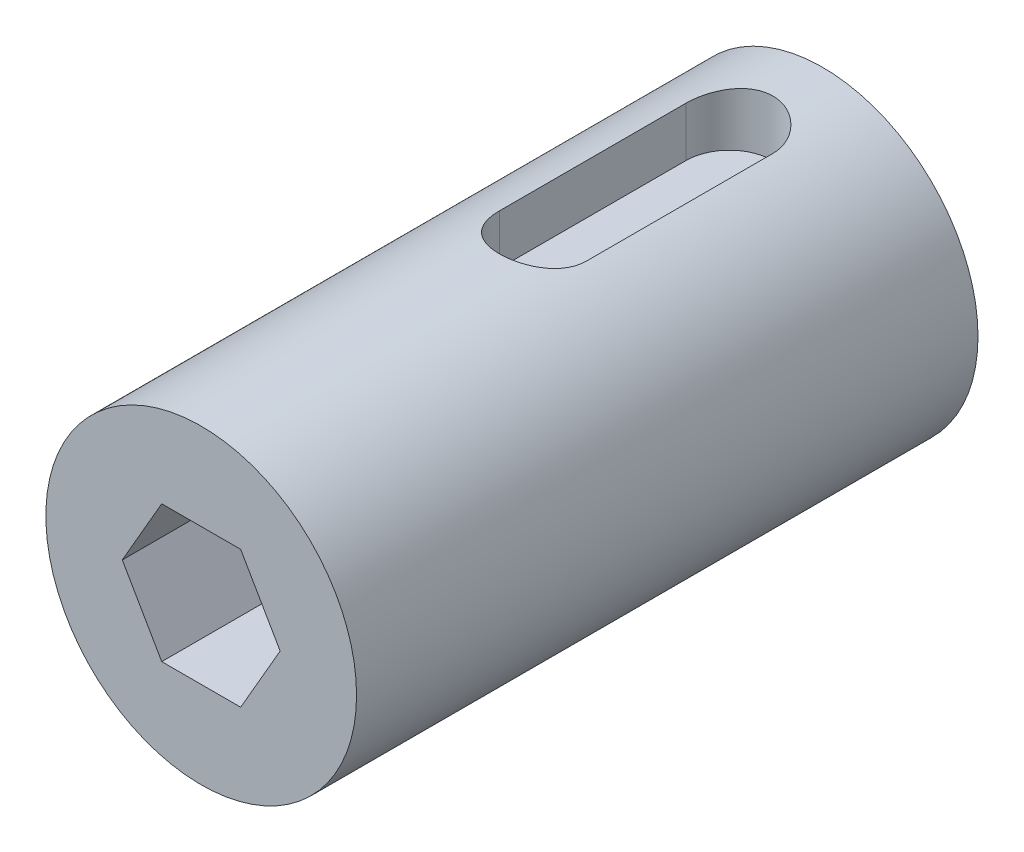
SolidWorks part; units mm, degrees
ref_plane "Piano frontale" through (0, 0, 0) normal (0, 0, 1) x (1, 0, 0)
ref_plane "Piano superiore" through (0, 0, 0) normal (0, 1, 0) x (1, 0, 0)
ref_plane "Piano destro" through (0, 0, 0) normal (1, 0, 0) x (0, 0, -1)
sketch "Schizzo1" plane through (0, 0, 0) normal (0, 0, 1) x (1, 0, 0)
  circle A0 centre (0, 0) radius 12.5
  dimension "D1" = 25
extrude "Estrusione-Estrusione1" add sketch "Schizzo1" along normal blind 50
sketch "Schizzo2" plane through (0, 0, 50) normal (0, 0, 1) x (1, 0, 0)
  line L1 (-3.1754, 5.5) -> (-6.3509, 0)
  line L2 (-6.3509, 0) -> (-3.1754, -5.5)
  line L3 (-3.1754, -5.5) -> (3.1754, -5.5)
  line L4 (3.1754, -5.5) -> (6.3509, 0)
  line L5 (6.3509, 0) -> (3.1754, 5.5)
  line L6 (3.1754, 5.5) -> (-3.1754, 5.5)
  circle A0 centre (0, 0) radius 5.5 construction
  dimension "D1" = 11
extrude "Taglio-Estrusione1" cut sketch "Schizzo2" against normal blind 15
sketch "Schizzo3" plane through (0, 0, 0) normal (0, 1, 0) x (1, 0, 0)
  line L0 (0, -7.5) -> (0, -22.5) construction
  line L1 (3.5, -7.5) -> (3.5, -22.5)
  line L2 (-3.5, -7.5) -> (-3.5, -22.5)
  arc A0 (3.5, -7.5) -> (-3.5, -7.5) centre (0, -7.5) ccw
  arc A1 (-3.5, -22.5) -> (3.5, -22.5) centre (0, -22.5) ccw
  point P3 (0, -15)
  dimension "D1" = 15
  dimension "D2" = 15
  dimension "D3" = 7
extrude "Taglio-Estrusione3" cut sketch "Schizzo3" against normal blind 15 from offset 23
